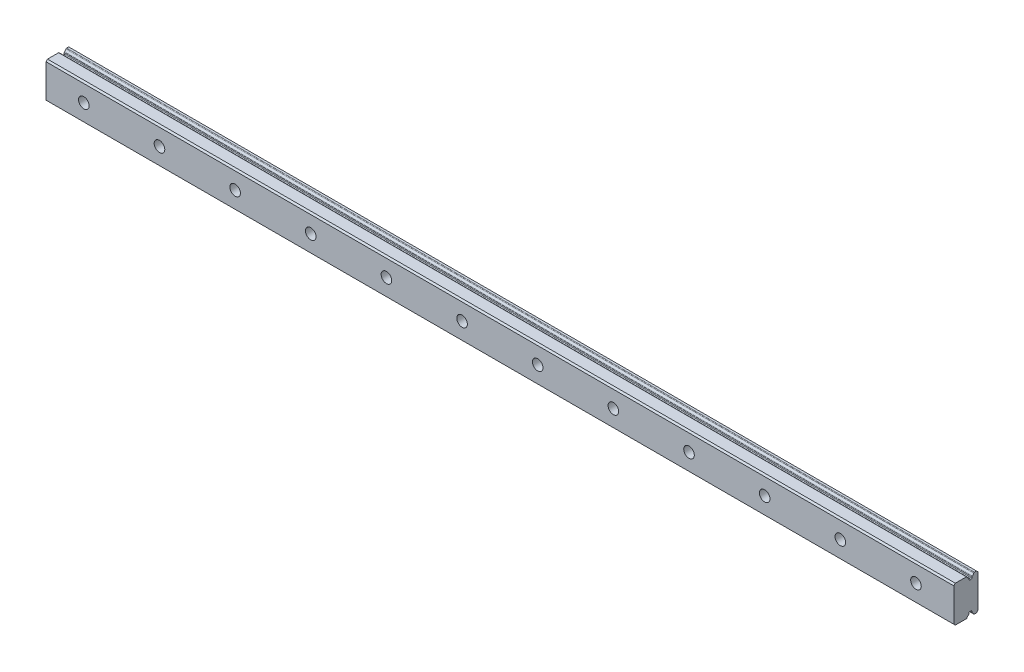
SolidWorks part; units mm, degrees
ref_plane "Plan de face" through (0, 0, 0) normal (0, 0, 1) x (1, 0, 0)
ref_plane "Plan de dessus" through (0, 0, 0) normal (0, 1, 0) x (1, 0, 0)
ref_plane "Plan de droite" through (0, 0, 0) normal (1, 0, 0) x (0, 0, -1)
ref_plane "Plan1" through (-167.5, 0, 0) normal (-1, 0, 0) x (0, -1, 0)
sketch "Esquisse1" plane through (-167.5, 0, 0) normal (-1, 0, 0) x (0, -1, 0)
  line L0 (-157, 193.75) -> (-168, 193.75)
  line L1 (-168, 193.75) -> (-168.5, 193.25)
  line L2 (-168.5, 193.25) -> (-168.5, 189.6079)
  line L3 (-167.5738, 188.7555) -> (-167.2282, 188.7253)
  line L4 (-167, 188.4762) -> (-167, 188.0238)
  line L5 (-167.2282, 187.7747) -> (-167.5948, 187.7427)
  line L6 (-168.5, 186.9246) -> (-168.5, 186.25)
  line L7 (-168.5, 186.25) -> (-168, 185.75)
  line L8 (-168, 185.75) -> (-157, 185.75)
  line L9 (-157, 185.75) -> (-156.5, 186.25)
  line L10 (-156.5, 186.25) -> (-156.5, 186.9246)
  line L11 (-157.4052, 187.7427) -> (-157.7718, 187.7747)
  line L12 (-158, 188.0238) -> (-158, 188.4762)
  line L13 (-157.7718, 188.7253) -> (-157.4262, 188.7555)
  line L14 (-156.5, 189.6079) -> (-156.5, 193.25)
  line L15 (-156.5, 193.25) -> (-157, 193.75)
  arc A0 (-168.5, 189.6079) -> (-168.3448, 189.3766) centre (-168.25, 189.6079) ccw
  arc A1 (-168.3448, 189.3766) -> (-167.7672, 188.8772) centre (-168.8, 188.2662) cw
  arc A2 (-167.7672, 188.8772) -> (-167.5738, 188.7555) centre (-167.552, 189.0045) ccw
  arc A3 (-167.2282, 188.7253) -> (-167, 188.4762) centre (-167.25, 188.4762) cw
  arc A4 (-167, 188.0238) -> (-167.2282, 187.7747) centre (-167.25, 188.0238) cw
  arc A5 (-167.5948, 187.7427) -> (-167.7845, 187.6268) centre (-167.573, 187.4936) ccw
  arc A6 (-167.7845, 187.6268) -> (-168.3448, 187.1559) centre (-168.8, 188.2662) cw
  arc A7 (-168.3448, 187.1559) -> (-168.5, 186.9246) centre (-168.25, 186.9246) ccw
  arc A8 (-156.5, 186.9246) -> (-156.6552, 187.1559) centre (-156.75, 186.9246) ccw
  arc A9 (-156.6552, 187.1559) -> (-157.2155, 187.6268) centre (-156.2, 188.2662) cw
  arc A10 (-157.2155, 187.6268) -> (-157.4052, 187.7427) centre (-157.427, 187.4936) ccw
  arc A11 (-157.7718, 187.7747) -> (-158, 188.0238) centre (-157.75, 188.0238) cw
  arc A12 (-158, 188.4762) -> (-157.7718, 188.7253) centre (-157.75, 188.4762) cw
  arc A13 (-157.4262, 188.7555) -> (-157.2328, 188.8772) centre (-157.448, 189.0045) ccw
  arc A14 (-157.2328, 188.8772) -> (-156.6552, 189.3766) centre (-156.2, 188.2662) cw
  arc A15 (-156.6552, 189.3766) -> (-156.5, 189.6079) centre (-156.75, 189.6079) ccw
extrude "Boss.-Extru.1" add sketch "Esquisse1" against normal blind 300
hole_wizard "Chambrage pour vis à tête hexagonale M31" positions "Esquisse3" profile "Esquisse2" counterbore size "M3" standard "Ansi Metric"
sketch "Esquisse3" plane through (0, 0, 185.75) normal (0, 0, -1) x (-1, 0, 0)
  line L1 (-132.5, 156.5) -> (167.5, 156.5) construction
  line L2 (167.5, 168) -> (167.5, 157) construction
  line L3 (155, 162.5) -> (130, 162.5) construction
  line L4 (130, 162.5) -> (105, 162.5) construction
  line L5 (105, 162.5) -> (80, 162.5) construction
  line L6 (80, 162.5) -> (55, 162.5) construction
  line L7 (55, 162.5) -> (30, 162.5) construction
  line L8 (30, 162.5) -> (5, 162.5) construction
  line L9 (5, 162.5) -> (-20, 162.5) construction
  line L10 (-20, 162.5) -> (-45, 162.5) construction
  line L11 (-45, 162.5) -> (-70, 162.5) construction
  line L12 (-70, 162.5) -> (-95, 162.5) construction
  line L13 (-95, 162.5) -> (-120, 162.5) construction
  point P0 (155, 162.5)
  point P1 (130, 162.5)
  point P2 (105, 162.5)
  point P3 (80, 162.5)
  point P4 (55, 162.5)
  point P5 (30, 162.5)
  point P6 (5, 162.5)
  point P7 (-20, 162.5)
  point P8 (-45, 162.5)
  point P9 (-70, 162.5)
  point P10 (-95, 162.5)
  point P11 (-120, 162.5)
  point P12 (-147.5, 162.5)
  dimension "D1" = 6
  dimension "D2" = 12.5
  dimension "D3" = 25
sketch "Esquisse2" plane through (-155, 162.5, 185.75) normal (1, 0, 0) x (0, 1, 0)
  line L0 (0, 0) -> (0, 8)
  line L1 (0, 8) -> (1.75, 8)
  line L3 (1.75, 8) -> (1.75, 4.5)
  line L4 (1.75, 4.5) -> (3, 4.5)
  line L5 (3, 4.5) -> (3, 0)
  line L7 (3, 0) -> (0, 0)
  line L11 (0, -6.35) -> (0, 107.95) construction
  dimension "Diamètre du perçage jusqu'au prochain" = 3.5
  dimension "Profondeur du perçage jusqu'au prochain" = 8
  dimension "Diamètre du chambrage" = 6
  dimension "Profondeur du chambrage" = 4.5
